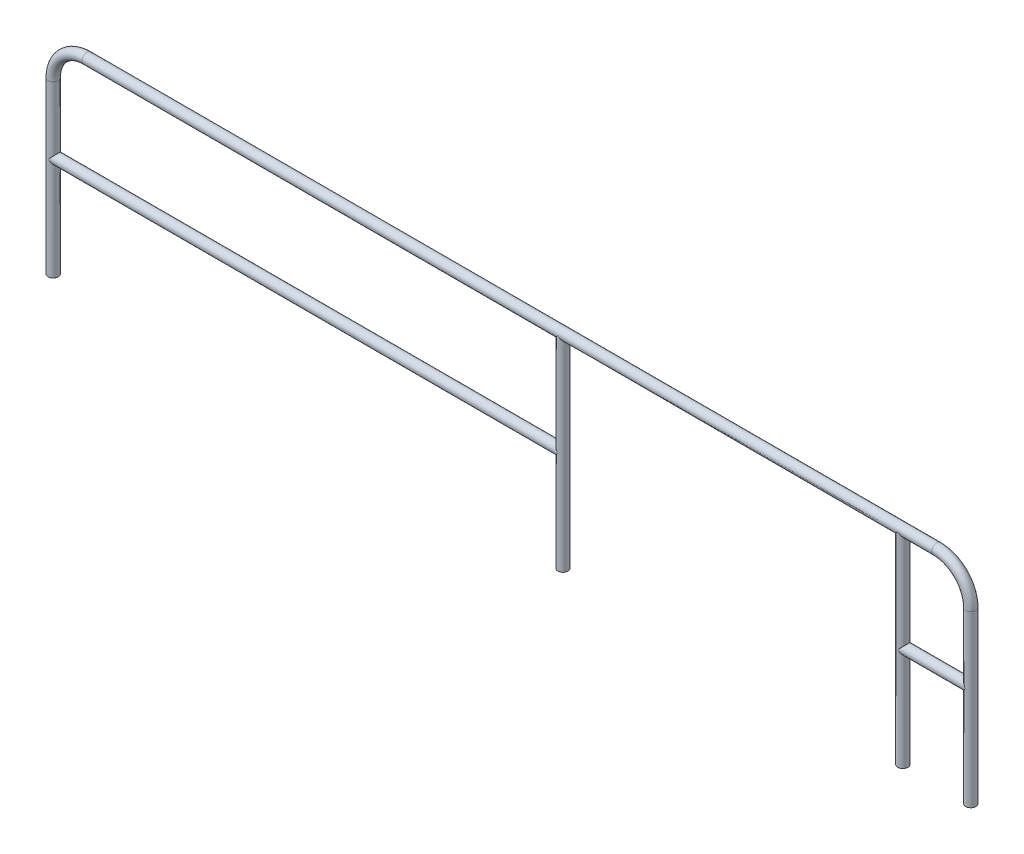
SolidWorks part; units mm, degrees
ref_plane "前视基准面" through (0, 0, 0) normal (0, 0, 1) x (1, 0, 0)
ref_plane "上视基准面" through (0, 0, 0) normal (0, 1, 0) x (1, 0, 0)
ref_plane "右视基准面" through (0, 0, 0) normal (1, 0, 0) x (0, 0, -1)
sketch "草图1" plane through (0, 0, 0) normal (0, 0, 1) x (1, 0, 0)
  line L1 (50, 0) -> (50, 25)
  line L2 (45, 30) -> (-80, 30)
  line L3 (-85, 25) -> (-85, 0)
  arc A0 (-80, 30) -> (-85, 25) centre (-80, 25) ccw
  arc A1 (50, 25) -> (45, 30) centre (45, 25) ccw
  dimension "D4" = 10
  dimension "D1" = 135
  dimension "D2" = 50
  dimension "D3" = 30
sketch "草图2" plane through (0, 0, 0) normal (0, 1, 0) x (1, 0, 0)
  circle A0 centre (-85, 0) radius 0.75
sweep "扫描1" add profiles "草图2" path "草图1"
sketch "草图4" plane through (0, 0, 0) normal (0, 1, 0) x (1, 0, 0)
  circle A0 centre (0, 0) radius 0.75
sketch "草图12" plane through (0, 0, 0) normal (1, 0, 0) x (0, 0, -1)
  line L0 (0, 0) -> (0, 15)
  circle A0 centre (0, 15) radius 0.75
  dimension "D1" = 15
sketch "草图13" plane through (0, 0, 0) normal (0, 1, 0) x (1, 0, 0)
  line L0 (50, 0) -> (40, 0)
  circle A0 centre (40, 0) radius 0.75
  dimension "D1" = 10
extrude "凸台-拉伸7" add sketch "草图13" along normal blind 30
sketch "草图11" plane through (0, 0, 0) normal (1, 0, 0) x (0, 0, -1)
  line L0 (0, 0) -> (0, 12.8743)
sketch "草图14" plane through (0, 0, 0) normal (0, 1, 0) x (-1, 0, 0)
  line L0 (85, 0) -> (10, 0)
  circle A0 centre (10, 0) radius 0.75
  dimension "D1" = 75
extrude "凸台-拉伸8" add sketch "草图14" along normal blind 30
ref_plane "基准面1" through (-85, 0, 0) normal (1, 0, 0) x (0, 0, -1)
sketch "草图15" plane through (-85, 0, 0) normal (1, 0, 0) x (0, 0, -1)
  line L0 (0, 0) -> (0, 15)
  circle A0 centre (0, 15) radius 0.75
  dimension "D1" = 15
extrude "凸台-拉伸9" add sketch "草图15" along normal blind 75
sketch "草图16" plane through (0, 0, 0) normal (0, 0, 1) x (1, 0, 0)
  line L0 (50, 15) -> (40.1605, 15)
  line L1 (50, 0) -> (50, 25) construction
  dimension "D1" = 15
ref_plane "基准面2" through (50, 15, 0) normal (-1, 0, 0) x (0, 0, 1)
sketch "草图17" plane through (50, 15, 0) normal (-1, 0, 0) x (0, 0, 1)
  circle A0 centre (0, 0) radius 0.75
extrude "凸台-拉伸10" add sketch "草图17" along normal blind 10
